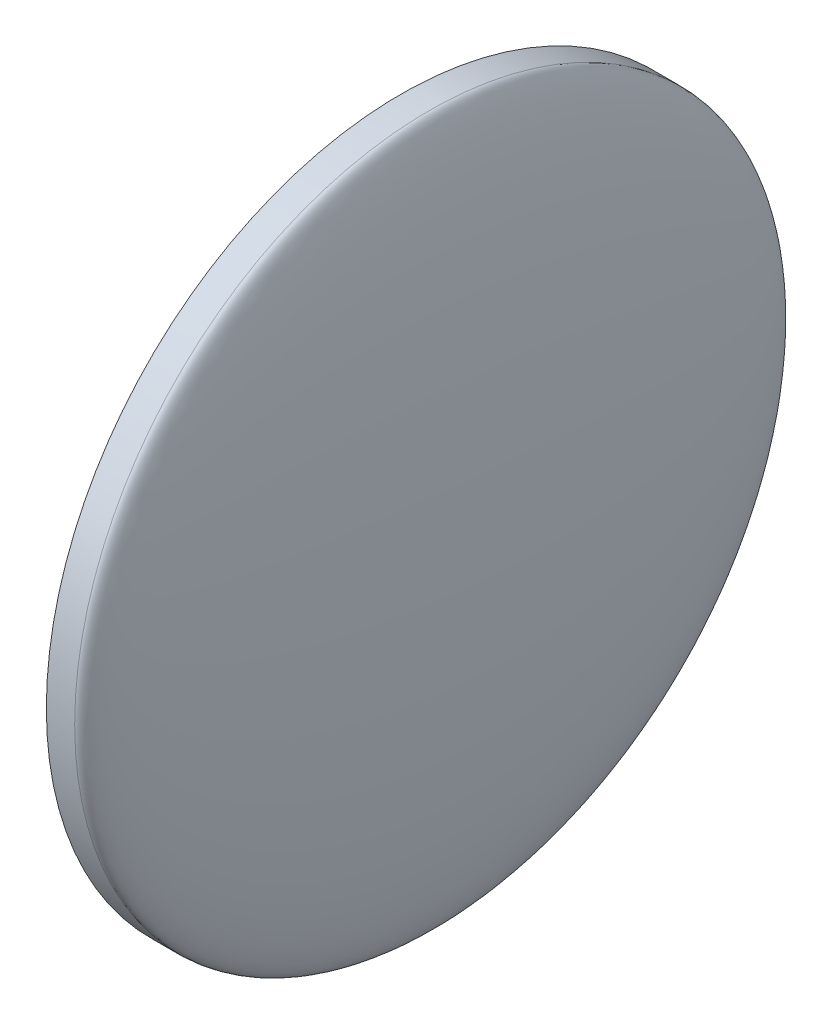
SolidWorks part; units mm, degrees
material "Glass"
ref_plane "Front Plane" through (0, 0, 0) normal (0, 0, 1) x (1, 0, 0)
ref_plane "Top Plane" through (0, 0, 0) normal (0, 1, 0) x (1, 0, 0)
ref_plane "Right Plane" through (0, 0, 0) normal (1, 0, 0) x (0, 0, -1)
sketch "Sketch1" plane through (0, 0, 0) normal (0, 1, 0) x (1, 0, 0)
  line L0 (1, 0) -> (2.2738, 0)
  line L1 (0, 0) -> (1, 0)
  line L2 (0, 0) -> (0, 12.5)
  line L3 (0, 12.5) -> (1, 12.5)
  line L4 (1, 0) -> (1, 12.5)
  ellipse E0 centre (1, 0) end of major axis (1, 12.5) minor radius 1.2738 (1, 12.5) -> (2.2738, 0) cw
revolve "Revolve1" add sketch "Sketch1" angle 360 about L1
